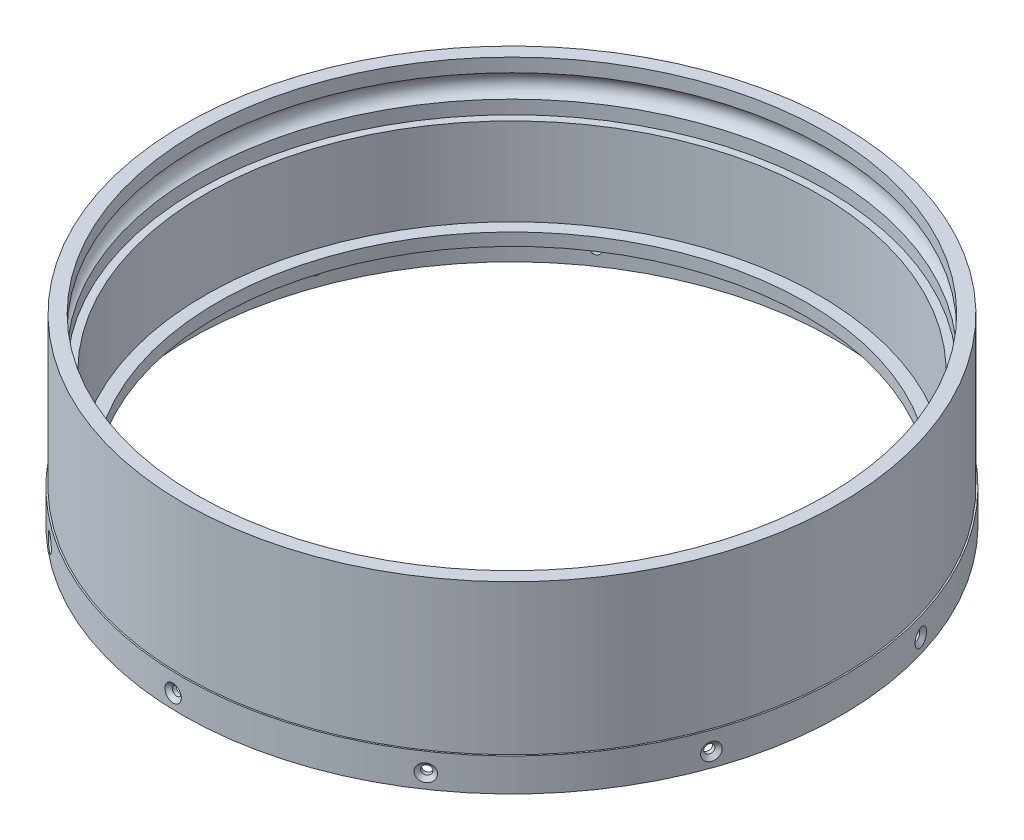
SolidWorks part; units mm, degrees
ref_plane "Front Plane" through (0, 0, 0) normal (0, 0, 1) x (1, 0, 0)
ref_plane "Top Plane" through (0, 0, 0) normal (0, 1, 0) x (1, 0, 0)
ref_plane "Right Plane" through (0, 0, 0) normal (1, 0, 0) x (0, 0, -1)
sketch "Sketch2" plane through (0, 0, 0) normal (1, 0, 0) x (0, 0, -1)
  line L0 (0, 0) -> (0, -49.6639) construction
  line L1 (79.9922, -2.1925) -> (79.9922, -5.6325)
  line L2 (79.9922, -2.1925) -> (83.439, -2.1925)
  line L3 (83.439, -2.1925) -> (83.439, -40.2925)
  line L7 (74.9122, -40.2925) -> (74.9122, -37.1175)
  line L8 (74.9122, -37.1175) -> (78.0872, -37.1175)
  line L9 (78.0872, -37.1175) -> (78.0872, -14.8925)
  line L10 (78.0872, -14.8925) -> (79.9922, -14.8925)
  line L11 (83.439, -40.2925) -> (83.82, -40.2925)
  line L12 (83.82, -40.2925) -> (83.82, -48.6745)
  line L13 (83.82, -48.6745) -> (81.9531, -48.6745)
  line L14 (81.9531, -40.2925) -> (74.9122, -40.2925)
  line L15 (81.9531, -48.6745) -> (81.9531, -40.2925)
  line L16 (79.9922, -11.4524) -> (79.9922, -14.8925)
  arc A0 (79.9922, -5.6325) -> (79.9922, -11.4524) centre (78.7222, -8.5425) cw
  point P18 (0, -24.8319)
  point P20 (0, 0)
  dimension "D1" = 83.82
  dimension "D8" = 3.175
  dimension "D9" = 1.27
  dimension "D2" = 83.439
  dimension "D3" = 3.4468
  dimension "D4" = 1.905
  dimension "D5" = 12.7
  dimension "D6" = 8.382
  dimension "D7" = 1.8669
  dimension "D10" = 38.1
  dimension "D11" = 8.382
  dimension "D12" = 3.175
  dimension "D13" = 3.175
revolve "Revolve1" add sketch "Sketch2" angle 360 about L0
hole_wizard "CSK for #2 Flat Head Machine Screw (100)1" positions "3DSketch1" profile "Sketch3" countersink size "#2" standard "ANSI Inch"
sketch3d "3DSketch1"
  point P0 (2.4133, -45.0085, -83.7853)
  point P12 (2.4133, -45.0085, -83.7853)
sketch "Sketch3" plane through (2.4133, -45.0085, -83.7853) normal (0, 1, 0) x (-0.9996, 0, -0.0288)
  line L0 (0, 0) -> (0, 76.8792)
  line L1 (0, 76.8792) -> (1.1303, 76.2)
  line L2 (1.1303, 76.2) -> (1.1303, 0.8845)
  line L3 (1.1303, 0.8845) -> (2.1844, 0)
  line L5 (2.1844, 0) -> (0, 0)
  line L6 (-1.1303, 0.8845) -> (-2.1844, 0) construction
  line L10 (0, 76.8792) -> (-1.1303, 76.2) construction
  line L11 (0, -6.35) -> (0, 107.95) construction
  dimension "Hole Dia." = 2.2606
  dimension "Hole Depth" = 76.2
  dimension "Near C'Sink Dia." = 4.3688
  dimension "Near C'Sink Angle" = 100
  dimension "Drill Angle" = 118
pattern_circular "CirPattern1" count 10 over 360 about axis through (0, 0, 0) along (0, 1, 0) of "CSK for #2 Flat Head Machine Screw (100)1"
